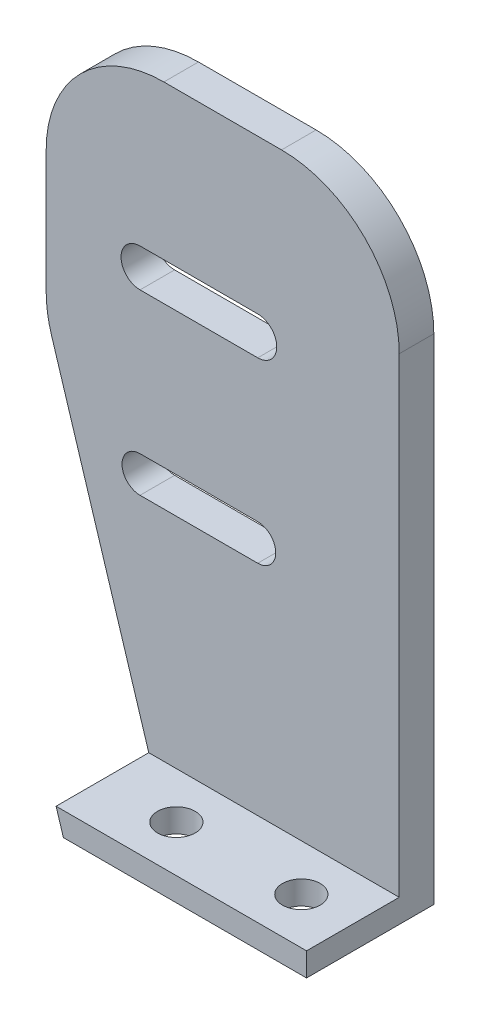
SolidWorks part; units mm, degrees
ref_plane "Front Plane" through (0, 0, 0) normal (0, 0, 1) x (1, 0, 0)
ref_plane "Top Plane" through (0, 0, 0) normal (0, 1, 0) x (1, 0, 0)
ref_plane "Right Plane" through (0, 0, 0) normal (1, 0, 0) x (0, 0, -1)
sketch "Sketch1" plane through (0, 0, 0) normal (0, 1, 0) x (1, 0, 0)
  line L1 (-15, 3.937) -> (15, 3.937)
  line L2 (-15, 3.937) -> (-15, -6.8776)
  line L3 (-15, -6.8776) -> (15, -6.8776)
  line L4 (15, 3.937) -> (15, -6.8776)
  point P0 (0, 0)
  dimension "D1" = 30
extrude "Boss-Extrude1" add sketch "Sketch1" along normal blind 2
sketch "Sketch2" plane through (0, 2, 0) normal (0, 1, 0) x (1, 0, 0)
  line L0 (-15, 3.937) -> (-15, -6.8776) construction
  line L1 (15, 3.937) -> (-15, 3.937)
  line L2 (15, 3.937) -> (15, 0.9987)
  line L3 (15, 0.9987) -> (-15, 0.9987)
  line L4 (-15, 3.937) -> (-15, 0.9987)
extrude "Boss-Extrude2" add sketch "Sketch2" along normal blind 50
sketch "Sketch3" plane through (0, 0, -3.937) normal (0, 0, -1) x (-1, 0, 0)
  line L0 (-2.9756, 37.3029) -> (7.0244, 37.3029) construction
  line L3 (-2.9756, 38.9181) -> (7.0244, 38.9181)
  line L6 (-2.9756, 35.6878) -> (7.0244, 35.6878)
  line L9 (-2.9756, 22.1029) -> (7.0244, 22.1029) construction
  line L12 (-2.9756, 23.6334) -> (7.0244, 23.6334)
  line L13 (-2.9756, 20.5725) -> (7.0244, 20.5725)
  arc A12 (-2.9756, 38.9181) -> (-2.9756, 35.6878) centre (-2.9756, 37.3029) ccw
  arc A13 (7.0244, 35.6878) -> (7.0244, 38.9181) centre (7.0244, 37.3029) ccw
  arc A14 (-2.9756, 23.6334) -> (-2.9756, 20.5725) centre (-2.9756, 22.1029) ccw
  arc A15 (7.0244, 20.5725) -> (7.0244, 23.6334) centre (7.0244, 22.1029) ccw
  point P6 (2.0244, 37.3029)
  point P12 (2.0244, 22.1029)
extrude "Cut-Extrude1" cut sketch "Sketch3" against normal through all
sketch "Sketch4" plane through (0, 2, 0) normal (0, 1, 0) x (1, 0, 0)
  line L0 (15, -2.9394) -> (-15, -2.9394) construction
  line L1 (15, -6.8776) -> (15, 0.9987) construction
  line L2 (-15, 0.9987) -> (-15, -6.8776) construction
  circle A0 centre (10.6189, -2.9394) radius 1.6
  circle A1 centre (0, -2.9394) radius 1.6
  dimension "D1" = 3.2
  dimension "D2" = 3.2
extrude "Cut-Extrude2" cut sketch "Sketch4" against normal up to next
sketch "Sketch5" plane through (0, 0, 0) normal (0, 0, 1) x (1, 0, 0)
  line L0 (-4.0809, -5.0809) -> (-16.9557, 36.3326)
  line L1 (-16.9557, 36.3326) -> (-18.5859, -5.0809)
  line L2 (-18.5859, -5.0809) -> (-4.0809, -5.0809)
extrude "Cut-Extrude3" cut sketch "Sketch5" along normal up to next and the other way up to next
fillet "Fillet1" radius 10 3 edges at (-15, 30.0418, -2.4678) (-15, 52, -2.4678) (15, 52, -2.4678)
